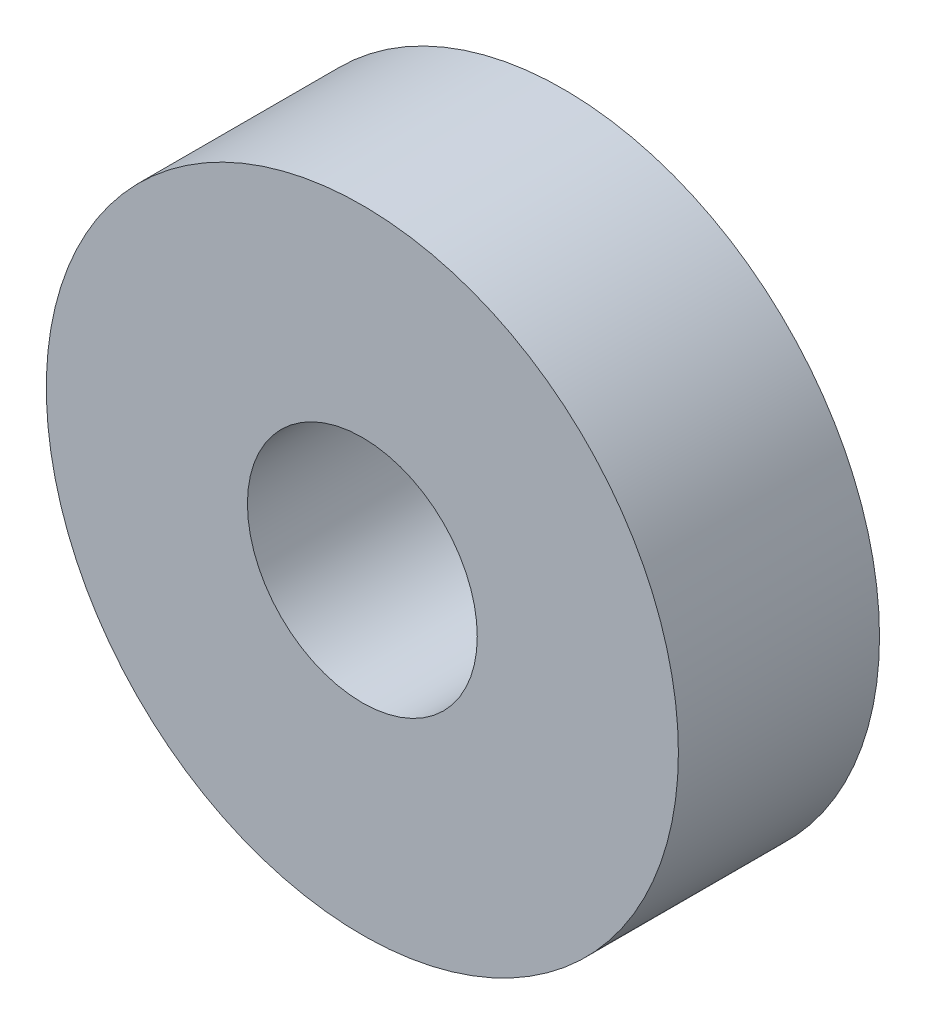
SolidWorks part; units mm, degrees
ref_plane "Front Plane" through (0, 0, 0) normal (0, 0, 1) x (1, 0, 0)
ref_plane "Top Plane" through (0, 0, 0) normal (0, 1, 0) x (1, 0, 0)
ref_plane "Right Plane" through (0, 0, 0) normal (1, 0, 0) x (0, 0, -1)
sketch "Sketch1" plane through (0, 0, 0) normal (0, 0, 1) x (1, 0, 0)
  circle A0 centre (0, 0) radius 4
  circle A1 centre (0, 0) radius 11
  dimension "D1" = 8
  dimension "D2" = 22
extrude "Boss-Extrude1" add sketch "Sketch1" along normal blind 7
